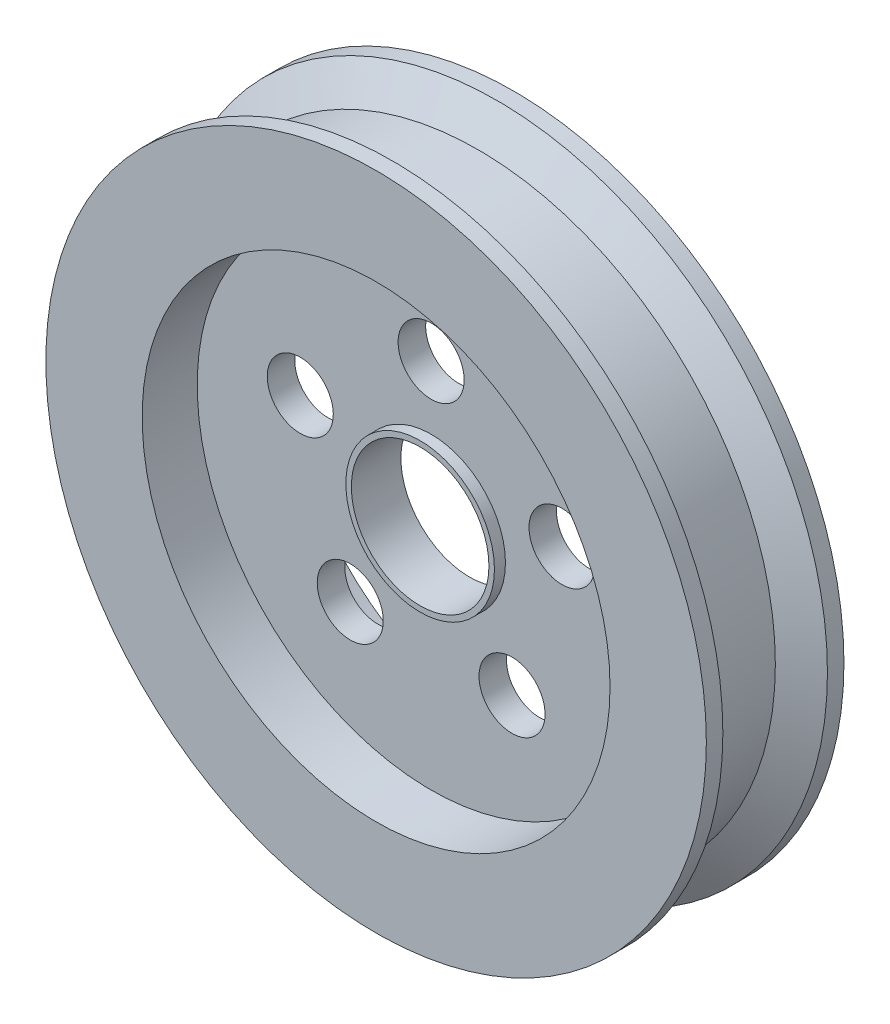
SolidWorks part; units mm, degrees
material "Stainless Steel (ferritic)"
ref_plane "Front Plane" through (0, 0, 0) normal (0, 0, 1) x (1, 0, 0)
ref_plane "Top Plane" through (0, 0, 0) normal (0, 1, 0) x (1, 0, 0)
ref_plane "Right Plane" through (0, 0, 0) normal (1, 0, 0) x (0, 0, -1)
sketch "Sketch1" plane through (0, 0, 0) normal (0, 0, 1) x (1, 0, 0)
  circle A0 centre (0, 0) radius 60
  circle A1 centre (0, 0) radius 12.5
  dimension "D1" = 120
  dimension "D2" = 25
extrude "Boss-Extrude1" add sketch "Sketch1" along normal mid plane 25
sketch "Sketch2" plane through (0, 0, 12.5) normal (0, 0, 1) x (1, 0, 0)
  circle A0 centre (0, 0) radius 42.5
  dimension "D1" = 85
extrude "Cut-Extrude1" cut sketch "Sketch2" against normal blind 10
mirror "Mirror1" about plane through (0, 0, 0) normal (0, 0, 1) of "Cut-Extrude1"
sketch "Sketch3" plane through (0, 0, 2.5) normal (0, 0, 1) x (1, 0, 0)
  circle A0 centre (0, 25) radius 6
  dimension "D1" = 12
  dimension "D2" = 25
extrude "Cut-Extrude2" cut sketch "Sketch3" against normal blind 10
pattern_circular "CirPattern1" count 5 over 360 about axis through (0, 0, 0) along (0, 0, 1) of "Cut-Extrude2"
sketch "Sketch4" plane through (0, 0, 0) normal (0, 1, 0) x (1, 0, 0)
  line L0 (0, 0) -> (0, 27.3313) construction
  line L1 (60, 9.5) -> (60, -9.5)
  line L2 (60, -12.5) -> (60, 12.5) construction
  line L3 (60, -9.5) -> (54, -6.0359)
  line L4 (54, -6.0359) -> (54, 6.0359)
  line L5 (54, 6.0359) -> (60, 9.5)
  line L6 (60, 12.5) -> (-60, 12.5) construction
  line L7 (-60, -12.5) -> (60, -12.5) construction
  dimension "D1" = 6
  dimension "D2" = 3
  dimension "D3" = 3
  dimension "D4" = 60
  dimension "D5" = 60
revolve "Cut-Revolve1" cut sketch "Sketch4" angle 360 about L0
sketch "Sketch5" plane through (0, 0, 2.5) normal (0, 0, 1) x (1, 0, 0)
  circle A1 centre (0, 0) radius 13.5
  circle A2 centre (0, 0) radius 12.5 construction
  circle A3 centre (0, 0) radius 12.5
  dimension "D1" = 27
extrude "Boss-Extrude2" add sketch "Sketch5" along normal blind 2 and the other way blind 7
